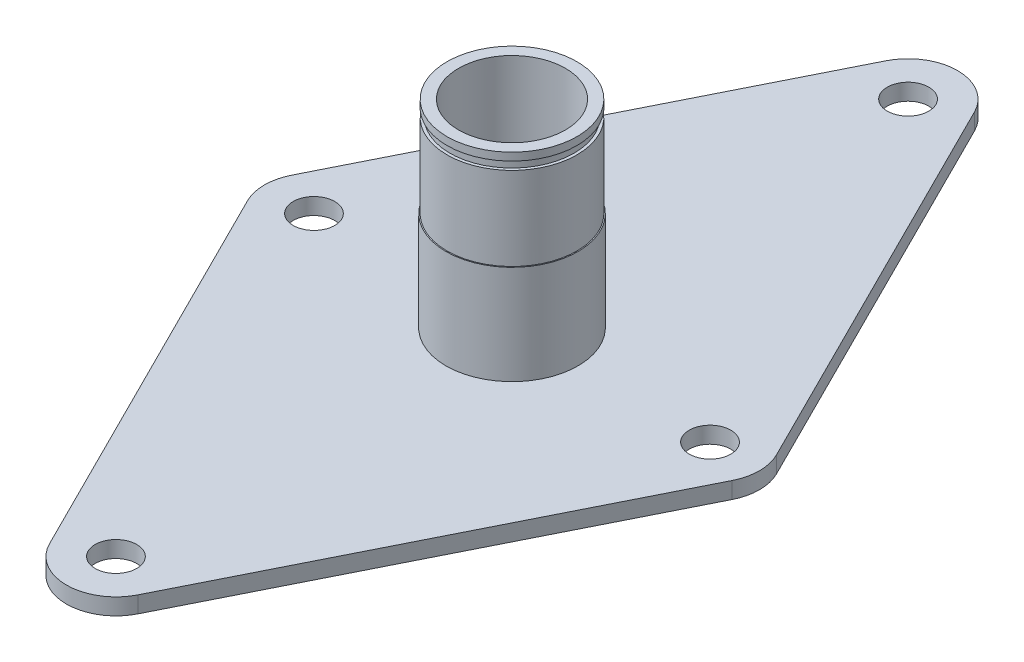
SolidWorks part; units mm, degrees
ref_plane "Front Plane" through (0, 0, 0) normal (0, 0, 1) x (1, 0, 0)
ref_plane "Top Plane" through (0, 0, 0) normal (0, 1, 0) x (1, 0, 0)
ref_plane "Right Plane" through (0, 0, 0) normal (1, 0, 0) x (0, 0, -1)
sketch "Sketch1" plane through (0, 0, 0) normal (0, 1, 0) x (1, 0, 0)
  line L0 (-8.5194, 80.4597) -> (-46.6194, 4.2597)
  line L1 (-46.6194, -4.2597) -> (-8.5194, -80.4597)
  line L2 (8.5194, -80.4597) -> (46.6194, -4.2597)
  line L3 (46.6194, 4.2597) -> (8.5194, 80.4597)
  circle A0 centre (0, 76.2) radius 4
  circle A1 centre (0, -76.2) radius 4
  circle A2 centre (-38.1, 0) radius 4
  circle A3 centre (38.1, 0) radius 4
  arc A4 (8.5194, 80.4597) -> (-8.5194, 80.4597) centre (0, 76.2) ccw
  arc A5 (-46.6194, 4.2597) -> (-46.6194, -4.2597) centre (-38.1, 0) ccw
  arc A6 (46.6194, -4.2597) -> (46.6194, 4.2597) centre (38.1, 0) ccw
  arc A7 (-8.5194, -80.4597) -> (8.5194, -80.4597) centre (0, -76.2) ccw
  point P0 (0, 76.2)
  point P1 (0, -76.2)
  point P2 (-38.1, 0)
  point P3 (38.1, 0)
extrude "Boss-Extrude1" add sketch "Sketch1" against normal blind 3.175
sketch "Sketch2" plane through (0, 0, 0) normal (0, 1, 0) x (1, 0, 0)
  circle A0 centre (0, 0) radius 12.7
extrude "Extrude-Thin1" add sketch "Sketch2" along normal blind 38.1 thin thin type one direction reverse wall 2.413
sketch "Sketch3" plane through (0, 38.1, 0) normal (0, 1, 0) x (1, 0, 0)
  circle A0 centre (0, 0) radius 12.75
  circle A1 centre (0, 0) radius 0.2
  circle A2 centre (0, 0) radius 12.5
  circle M1 centre (0, 0) radius 12.7
extrude "Cut-Extrude2" cut sketch "Sketch3" against normal blind 19.05 contours A2 M1
ref_plane "Plane1" through (0, 35.0632, 0) normal (0, -1, 0) x (-1, 0, 0)
sketch "Sketch4" plane through (0, 35.0632, 0) normal (0, -1, 0) x (-1, 0, 0)
  circle A0 centre (0, 0) radius 12.5
  circle A1 centre (0, 0) radius 11.95
extrude "Cut-Extrude3" cut sketch "Sketch4" against normal blind 1.55
